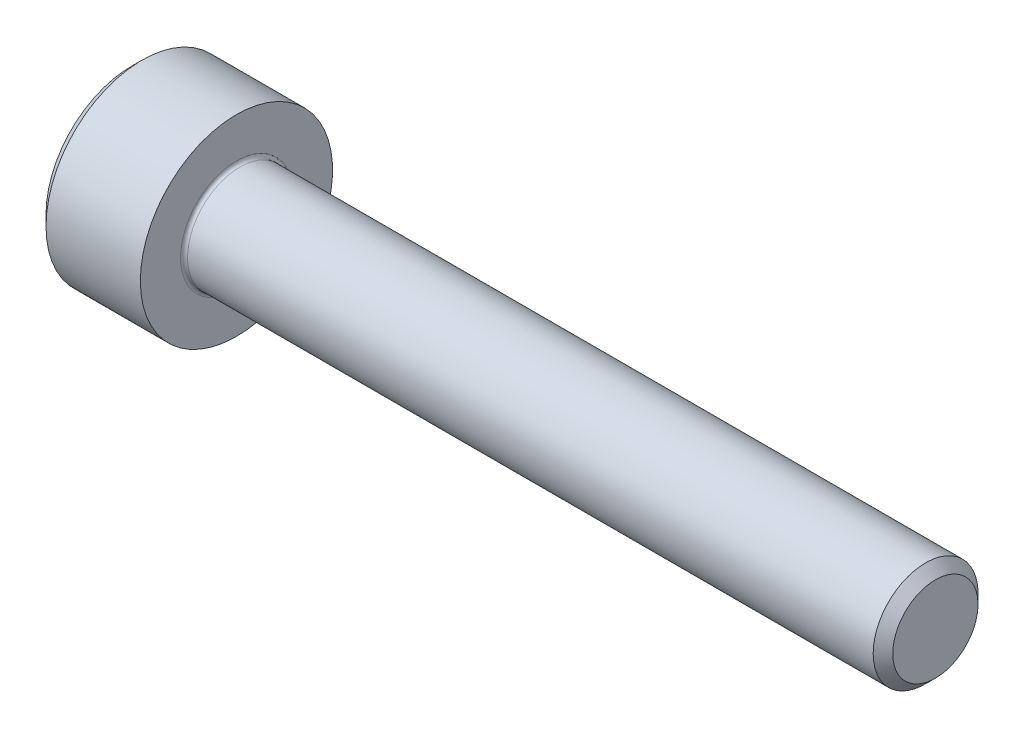
SolidWorks part; units mm, degrees
revolve "Base-Revolve" add sketch "BodySke"
sketch "BodySke" plane through (0, 0, 0) normal (0, 0, 1) x (1, 0, 0)
  line L0 (0, 0) -> (0, 2.45)
  line L1 (0.3, 2.75) -> (3, 2.75)
  line L2 (3, 2.75) -> (3, 1.5)
  line L3 (3, 1.5) -> (22.7195, 1.5)
  line L4 (23, 1.2195) -> (23, 0)
  line L5 (23, 0) -> (0, 0)
  line L6 (-31.75, 0) -> (127, 0) construction
  line L7 (0, 2.45) -> (0.3, 2.75)
  line L8 (23, 1.2195) -> (22.7195, 1.5)
  line L9 (0, -2.45) -> (0.3, -2.75) construction
  line L10 (23, -1.2195) -> (22.7195, -1.5) construction
  line L11 (3.5, 9.525) -> (3.5, 3.175) construction
  line L12 (3, 9.525) -> (3, 3.175) construction
  line L13 (-27, 9.525) -> (-27, 3.175) construction
  dimension "Diameter" = 3
  dimension "Head_ht" = 3
  dimension "Length" = 20
  dimension "Body_ch_ang" = 45
  dimension "Head_dia" = 5.5
  dimension "Head_ch_ang" = 45
  dimension "Minor_dia" = 2.439
  dimension "Advance" = 0.5
  dimension "Thread_nom" = 20
  dimension "Thread_length" = 50
  dimension "Head_ch_ht" = 0.3
cosmetic thread "ThreadCosmetic"
fillet "Fillet1" radius 0.1 1 edges at (3, 0, 1.5)
ref_plane "Plane1" through (0, 0, 0) normal (0, 0, 1) x (1, 0, 0)
ref_plane "Plane2" through (0, 0, 0) normal (0, 1, 0) x (1, 0, 0)
ref_plane "Plane3" through (0, 0, 0) normal (1, 0, 0) x (0, 0, -1)
sketch "Sketch2" plane through (0, 0, 0) normal (0, 0, 1) x (1, 0, 0)
  line L0 (0, 1.28) -> (1.3, 1.28)
  line L1 (1.3, 1.28) -> (2.039, 0)
  line L2 (-31.75, 0) -> (127, 0) construction
  line L3 (2.039, 0) -> (0, 0)
  line L4 (0, 0) -> (0, 1.28)
  line L5 (0, 2.45) -> (0, -2.45) construction
  line L6 (0, 0) -> (47.625, 0) construction
  line L7 (3, -2.75) -> (3, 2.75) construction
  dimension "D1" = 1.28
  dimension "D2" = 60
revolve "Hex-PreBroach" cut sketch "Sketch2" angle 360 about L6
sketch "Sketch3" plane through (0, 0, 0) normal (-1, 0, 0) x (0, 0.5, 0.866)
  line L0 (0.739, 1.28) -> (-0.739, 1.28)
  line L1 (-0.739, 1.28) -> (-1.478, 0)
  line L2 (0.739, 1.28) -> (1.478, 0)
  line L3 (0.739, -1.28) -> (1.478, 0)
  line L4 (0.739, -1.28) -> (-0.739, -1.28)
  line L5 (-0.739, -1.28) -> (-1.478, 0)
  dimension "D1" = 1.28
  dimension "D2" = 1.28
  dimension "Hex_size" = 2.56
extrude "Hex" cut sketch "Sketch3" against normal blind 1.3
sketch "Sketch4" plane through (0, 0, 0) normal (-1, 0, 0) x (0, 0, 1)
  line L0 (0, 0) -> (1.4605, 0)
  line L1 (0, 0) -> (6.1484, 3.5498) construction
  line L2 (0, 0) -> (0.7302, 1.2648)
  line L3 (1.2009, 0.3267) -> (1.3933, 0.4378)
  line L4 (0.8834, 0.8767) -> (1.0758, 0.9877)
  arc A0 (1.2009, 0.3267) -> (0.8834, 0.8767) centre (0, 0) ccw
  arc A1 (1.4605, 0) -> (1.3933, 0.4378) centre (0, 0) ccw
  arc A2 (0.7302, 1.2648) -> (1.0758, 0.9877) centre (0, 0) cw
  dimension "D1" = 30
  dimension "D2" = 60
  dimension "Spline_p_dim" = 0.635
  dimension "D3" = 0.3175
extrude "Spline" [suppressed] cut sketch "Sketch4" against normal blind 1.3
pattern_circular "CirPattern1" [suppressed] count 6 every 60
sketch "Sketch5" plane through (0, 0, 0) normal (0, 0, 1) x (1, 0, 0)
  line L0 (-31.75, 0) -> (127, 0) construction
  line L2 (0, 2.45) -> (0, -2.45) construction
  circle A0 centre (1.2, 0) radius 0.475
  dimension "Drilled_hole_dia" = 0.95
  dimension "Drilled_hole_loc" = 1.2
extrude "Hole" [suppressed] cut sketch "Sketch5" against normal through all and the other way through all
pattern_circular "Drilled-4" [suppressed] count 2 every 60
pattern_circular "Drilled-6" [suppressed] count 3 every 60
sketch "ThdSchSke" plane through (0, 0, 0) normal (0, 0, 1) x (1, 0, 0)
  line L0 (3.5, -1.2195) -> (3.3036, -1.5)
  line L1 (3.5, -1.2195) -> (3.6964, -1.5)
  line L2 (3.6964, -1.5) -> (3.6964, -1.875)
  line L3 (-3.175, 0) -> (5.1513, 0) construction
  line L5 (3.6964, -1.875) -> (3.3036, -1.875)
  line L6 (3.3036, -1.875) -> (3.3036, -1.5)
  line L7 (0, 2.45) -> (0, -2.45) construction
  dimension "Thread_minor" = 2.439
  dimension "Diameter" = 3
  dimension "Start" = 3.5
revolve "ThreadSchematic" [suppressed] cut sketch "ThdSchSke" angle 360 about L3
pattern_linear "ThdSchPat" [suppressed]
equation "\"D2@Sketch3\" = \"Hex_size@Sketch3\" / 2"
equation "\"D1@Sketch3\" = \"Hex_size@Sketch3\" / 2"
equation "\"D1@Sketch2\" = \"Hex_size@Sketch3\" / 2"
equation "\"D3@Sketch4\" = \"Spline_p_dim@Sketch4\" / 2"
equation "\"Thread_minor@ThreadCosmetic\"  =  \"Minor_dia@BodySke\""
equation "\"D2@CirPattern1\" = 360 / \"Num_teeth@CirPattern1\""
equation "\"Wall_thickness@Sketch2\" = \"Head_ht@BodySke\" - \"Key_eng@Hex\""
equation "\"Thread_length@ThreadCosmetic\" = ((sgn( (\"Length@BodySke\" - \"Advance@BodySke\" ) - \"Thread_nom@BodySke\" )-1)*( (\"Length@BodySke\" - \"Advance@BodySke\" ) - \"Thread_nom@BodySke\" ))/-2+ \"Thread_nom@BodySke\""
equation "\"Thread_minor@ThdSchSke\" = \"Minor_dia@BodySke\""
equation "\"Diameter@ThdSchSke\" = \"Diameter@BodySke\""
equation "\"Overcut@ThdSchSke\" = \"Diameter@BodySke\" * 1.25"
equation "\"Start@ThdSchSke\" = \"Head_ht@BodySke\" + \"Length@BodySke\" - \"Thread_length@ThreadCosmetic\"  '---Non-countersunk---"
equation "\"Num_threads@ThdSchPat\" = int( \"Thread_length@ThreadCosmetic\" / \"Advance@BodySke\" + 0.999 )  + 1"
equation "\"Advance@ThdSchPat\" = \"Thread_length@ThreadCosmetic\" /  (\"Num_threads@ThdSchPat\" - 1) 'relax it"
equation "\"Num_threads@ThdSchPat\" = \"Num_threads@ThdSchPat\" - sgn( \"Num_threads@ThdSchPat\" - 1) '---chamfered tips only---"
